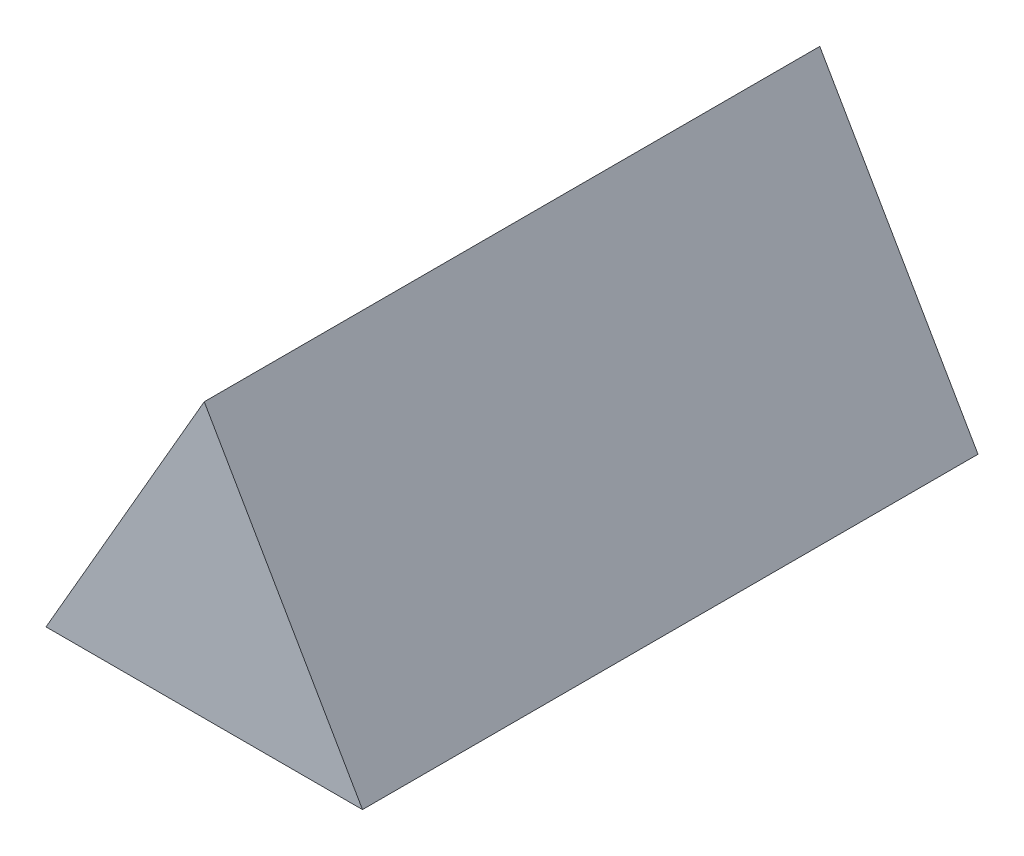
SolidWorks part; units mm, degrees
ref_plane "Piano frontale" through (0, 0, 0) normal (0, 0, 1) x (1, 0, 0)
ref_plane "Piano superiore" through (0, 0, 0) normal (0, 1, 0) x (1, 0, 0)
ref_plane "Piano destro" through (0, 0, 0) normal (1, 0, 0) x (0, 0, -1)
sketch "Schizzo1" plane through (0, 0, 0) normal (0, 0, 1) x (1, 0, 0)
  line L1 (0, 47.5) -> (-41.1362, -23.75)
  line L2 (-41.1362, -23.75) -> (41.1362, -23.75)
  line L3 (41.1362, -23.75) -> (0, 47.5)
  circle A0 centre (0, 0) radius 23.75 construction
  dimension "D1" = 47.5
extrude "Estrusione-Estrusione1" add sketch "Schizzo1" along normal blind 160
